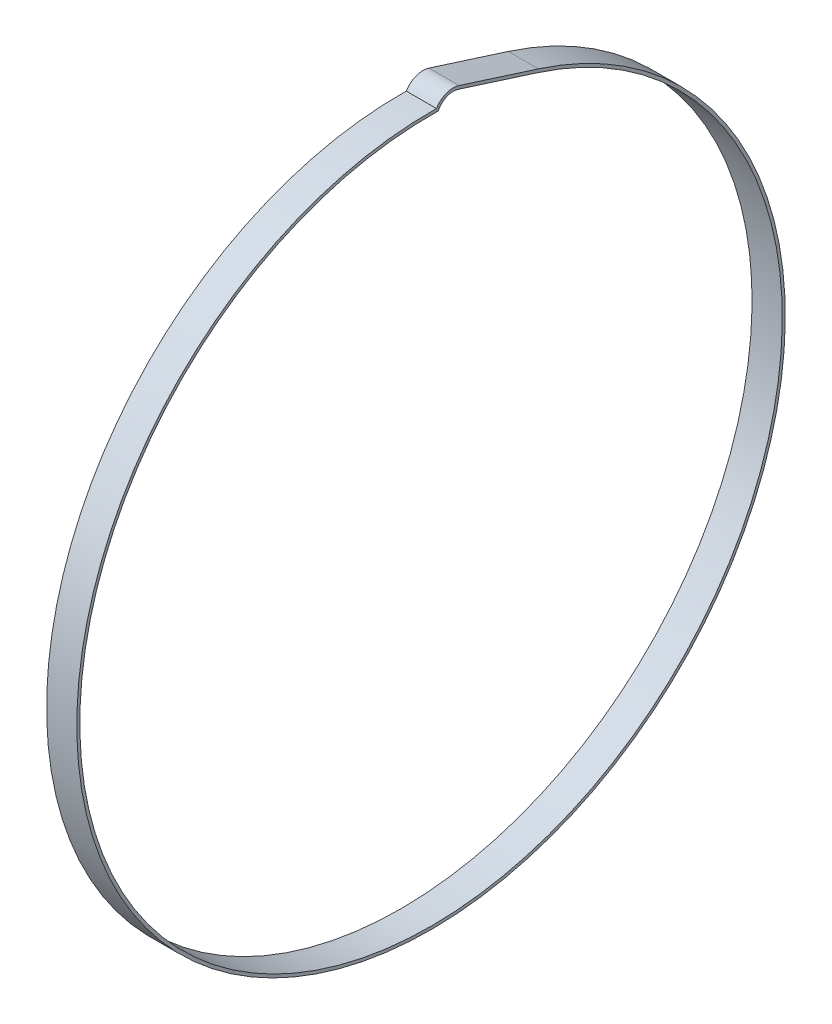
SolidWorks part; units mm, degrees
ref_plane "Front Plane" through (0, 0, 0) normal (0, 0, 1) x (1, 0, 0)
ref_plane "Top Plane" through (0, 0, 0) normal (0, 1, 0) x (1, 0, 0)
ref_plane "Right Plane" through (0, 0, 0) normal (1, 0, 0) x (0, 0, -1)
sketch "Sketch1" plane through (0, 0, 0) normal (1, 0, 0) x (0, 0, -1)
  line L0 (0, 0) -> (0, 204.895) construction
  line L2 (45.1725, 141.957) -> (11.797, 152.5776)
  line L3 (44.7874, 140.7468) -> (11.4119, 151.3674)
  arc A0 (3.0395, 147.6697) -> (44.7874, 140.7468) centre (0, 0) ccw
  arc A2 (11.4119, 151.3674) -> (3.0395, 147.6697) centre (9.3169, 144.7836) ccw
  arc A5 (2.2806, 148.9535) -> (45.1725, 141.957) centre (0, 0) ccw
  arc A6 (11.797, 152.5776) -> (2.2806, 148.9535) centre (9.3169, 144.7836) ccw
  dimension "D1" = 295.402
  dimension "D2" = 1.27
extrude "Boss-Extrude1" add sketch "Sketch1" along normal blind 12.7
